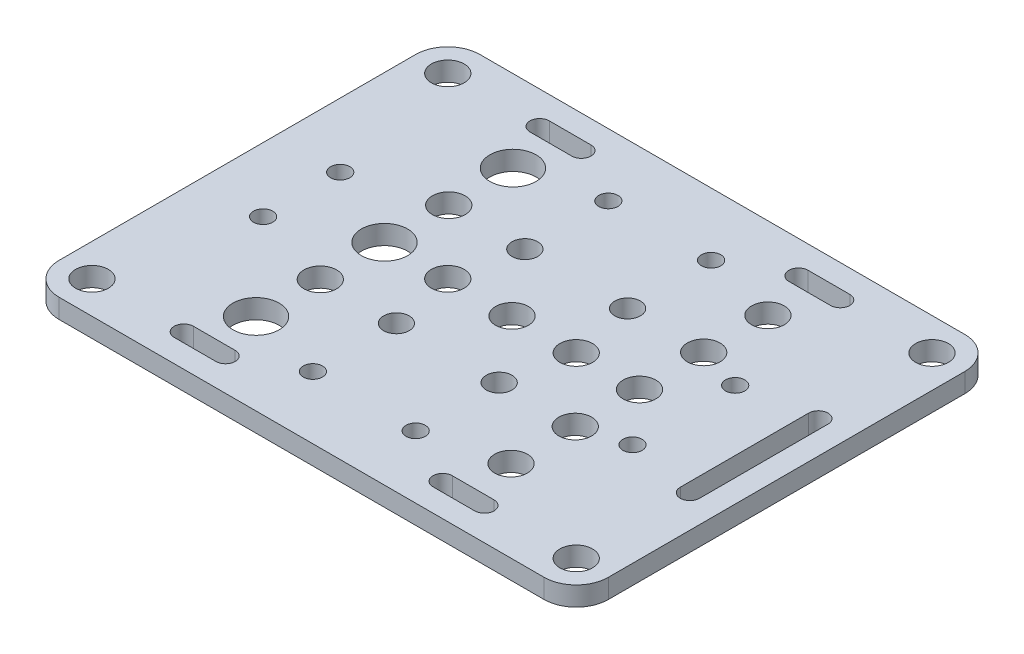
SolidWorks part; units mm, degrees
material "6061-T6 (SS)"
ref_plane "Front Plane" through (0, 0, 0) normal (0, 0, 1) x (1, 0, 0)
ref_plane "Top Plane" through (0, 0, 0) normal (0, 1, 0) x (1, 0, 0)
ref_plane "Right Plane" through (0, 0, 0) normal (1, 0, 0) x (0, 0, -1)
sketch "Sketch1" plane through (0, 0, 0) normal (0, 1, 0) x (1, 0, 0)
  line L0 (0, 0) -> (32.75, 0) construction
  line L1 (27.75, -32.75) -> (-27.75, -32.75)
  line L2 (37.7, 10) -> (37.7, -10) construction
  line L3 (27.75, 32.75) -> (-27.75, 32.75)
  line L4 (39.2, 10) -> (39.2, -10)
  line L5 (0, 32.75) -> (0, 0) construction
  line L6 (-31.2855, 31.2855) -> (31.8713, -31.8713) construction
  line L7 (31.2855, 31.2855) -> (-31.8713, -31.8713) construction
  line L8 (-42.75, -27.75) -> (-42.75, 27.75)
  line L9 (42.75, 27.75) -> (42.75, -27.75)
  line L10 (37.75, 32.75) -> (27.75, 32.75)
  line L11 (27.75, -32.75) -> (37.75, -32.75)
  line L12 (-27.75, -32.75) -> (-37.75, -32.75)
  line L13 (-37.75, 32.75) -> (-27.75, 32.75)
  line L14 (36.2, 10) -> (36.2, -10)
  line L15 (-16.9, 27.7) -> (-23.4, 27.7) construction
  line L16 (-16.9, 26.2) -> (-23.4, 26.2)
  line L17 (-16.9, 29.2) -> (-23.4, 29.2)
  line L18 (16.9, 27.7) -> (23.4, 27.7) construction
  line L19 (16.9, 26.2) -> (23.4, 26.2)
  line L20 (16.9, 29.2) -> (23.4, 29.2)
  line L21 (47.8379, 16.1225) -> (-48.4929, 16.1225) construction
  line L22 (-42.75, 0) -> (42.75, 0) construction
  line L24 (-16.9, -27.7) -> (-23.4, -27.7) construction
  line L25 (-16.9, -26.2) -> (-23.4, -26.2)
  line L26 (-16.9, -29.2) -> (-23.4, -29.2)
  line L30 (16.9, -27.7) -> (23.4, -27.7) construction
  line L31 (16.9, -26.2) -> (23.4, -26.2)
  line L32 (16.9, -29.2) -> (23.4, -29.2)
  circle A0 centre (37.7, 27.7) radius 2.55
  circle A1 centre (37.7, -27.7) radius 2.55
  circle A2 centre (-37.7, -27.7) radius 2.55
  circle A3 centre (-37.7, 27.7) radius 2.55
  circle A4 centre (-8, 23) radius 1.5
  circle A5 centre (-8, 10) radius 2
  circle A6 centre (0, 0) radius 2.55
  circle A7 centre (10, 0) radius 2.55
  circle A8 centre (-10, 0) radius 2.55
  circle A9 centre (-19.85, 20) radius 3.6
  circle A10 centre (-19.85, 0) radius 3.6
  circle A11 centre (-19.85, -20) radius 3.6
  circle A12 centre (8, 23) radius 1.5
  circle A13 centre (-8, -10) radius 2
  circle A14 centre (8, -10) radius 2
  circle A15 centre (8, 10) radius 2
  circle A16 centre (-19.85, 10) radius 2.55
  circle A17 centre (-8, -23) radius 1.5
  circle A18 centre (8, -23) radius 1.5
  circle A19 centre (-32.75, 6) radius 1.5
  arc A20 (39.2, 10) -> (36.2, 10) centre (37.7, 10) ccw
  arc A21 (36.2, -10) -> (39.2, -10) centre (37.7, -10) ccw
  arc A22 (37.75, 32.75) -> (42.75, 27.75) centre (37.75, 27.75) cw
  arc A23 (37.75, -32.75) -> (42.75, -27.75) centre (37.75, -27.75) ccw
  circle A24 centre (19.85, 20) radius 2.55
  circle A25 centre (19.85, 0) radius 2.55
  arc A26 (-37.75, -32.75) -> (-42.75, -27.75) centre (-37.75, -27.75) cw
  circle A27 centre (19.85, -20) radius 2.55
  arc A28 (-42.75, 27.75) -> (-37.75, 32.75) centre (-37.75, 27.75) cw
  circle A29 centre (-32.75, -6) radius 1.5
  circle A30 centre (26.75, 8) radius 1.5
  circle A31 centre (26.7667, -8) radius 1.5
  circle A46 centre (19.85, 10) radius 2.55
  circle A54 centre (19.85, -10) radius 2.55
  circle A63 centre (-19.85, -10) radius 2.55
  arc A71 (-16.9, 26.2) -> (-16.9, 29.2) centre (-16.9, 27.7) ccw
  arc A72 (-23.4, 29.2) -> (-23.4, 26.2) centre (-23.4, 27.7) ccw
  arc A73 (16.9, 26.2) -> (16.9, 29.2) centre (16.9, 27.7) cw
  arc A74 (23.4, 29.2) -> (23.4, 26.2) centre (23.4, 27.7) cw
  arc A77 (-16.9, -26.2) -> (-16.9, -29.2) centre (-16.9, -27.7) cw
  arc A78 (-23.4, -29.2) -> (-23.4, -26.2) centre (-23.4, -27.7) cw
  arc A81 (16.9, -26.2) -> (16.9, -29.2) centre (16.9, -27.7) ccw
  arc A82 (23.4, -29.2) -> (23.4, -26.2) centre (23.4, -27.7) ccw
  point P0 (0, 0)
  point P54 (37.7, 0)
  point P162 (-20.15, 27.7)
  point P170 (20.15, 27.7)
  point P184 (-20.15, -27.7)
  point P198 (20.15, -27.7)
  dimension "D3" = 13
  dimension "D5" = 7.2
  dimension "D7" = 8
  dimension "D10" = 10
  dimension "D19" = 13
  dimension "D4" = 13
  dimension "D11" = 8
  dimension "D12" = 3
  dimension "D13" = 4
  dimension "D15" = 8
  dimension "D17" = 8
  dimension "D18" = 13
  dimension "D20" = 85.5
  dimension "D21" = 5.05
  dimension "D22" = 5.05
  dimension "D23" = 5.1
  dimension "D24" = 5.05
  dimension "D25" = 5.05
  dimension "D8" = 5.05
  dimension "D9" = 5.05
  dimension "D26" = 5.05
  dimension "D29" = 5.05
  dimension "D30" = 5
  dimension "D31" = 5.05
  dimension "D32" = 16.1225
  dimension "D33" = 12
  dimension "D35" = 10
  dimension "D36" = 8
  dimension "D37" = 2
  dimension "D38" = 16
  dimension "D1" = 65.5
  dimension "D6" = 40
  dimension "D14" = 10
  dimension "D16" = 39.7
  dimension "D27" = 6.5
  dimension "D28" = 3
  dimension "D34" = 6
extrude "Boss-Extrude1" add sketch "Sketch1" along normal blind 3
